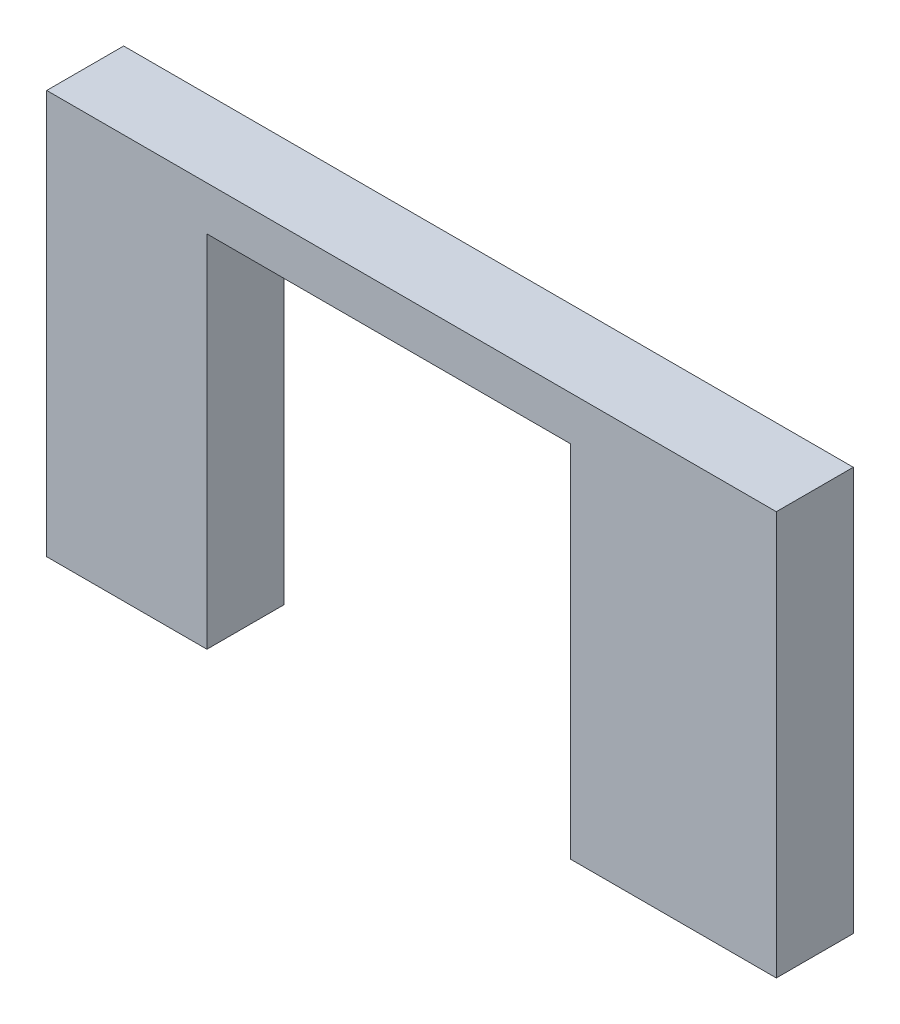
SolidWorks part; units mm, degrees
ref_plane "Front Plane" through (0, 0, 0) normal (0, 0, 1) x (1, 0, 0)
ref_plane "Top Plane" through (0, 0, 0) normal (0, 1, 0) x (1, 0, 0)
ref_plane "Right Plane" through (0, 0, 0) normal (1, 0, 0) x (0, 0, -1)
sketch "Sketch1" plane through (0, 0, 0) normal (0, 0, 1) x (1, 0, 0)
  line L1 (0, 0) -> (30.1, 0)
  line L2 (0, 0) -> (0, 16.66)
  line L3 (0, 16.66) -> (30.1, 16.66)
  line L4 (30.1, 0) -> (30.1, 16.66)
extrude "Boss-Extrude1" add sketch "Sketch1" along normal blind 3.175
sketch "Sketch2" plane through (0, 0, 3.175) normal (0, 0, 1) x (1, 0, 0)
  line L1 (6.61, 14.84) -> (21.61, 14.84)
  line L2 (6.61, 14.84) -> (6.61, -0.16)
  line L3 (6.61, -0.16) -> (21.61, -0.16)
  line L4 (21.61, 14.84) -> (21.61, -0.16)
  line L5 (30.1, 0) -> (30.1, 16.66) construction
  line L6 (30.1, 16.66) -> (0, 16.66) construction
  dimension "D1" = 15
  dimension "D2" = 8.49
  dimension "D3" = 1.82
  dimension "D4" = 15
extrude "Cut-Extrude1" cut sketch "Sketch2" against normal through all
